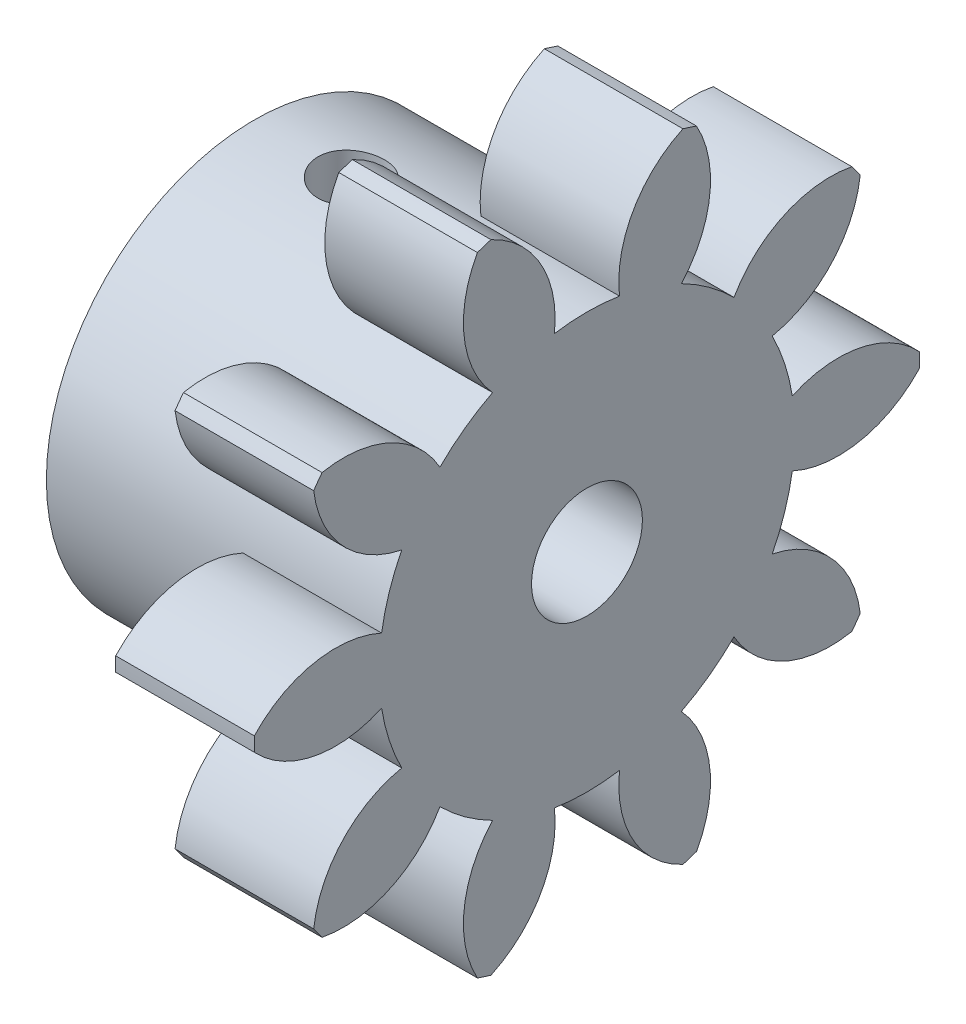
SolidWorks part; units mm, degrees
ref_plane "Plane1" through (0, 0, 0) normal (0, 0, 1) x (1, 0, 0)
ref_plane "Plane2" through (0, 0, 0) normal (0, 1, 0) x (1, 0, 0)
ref_plane "Plane3" through (0, 0, 0) normal (1, 0, 0) x (0, 0, -1)
sketch "HoldingSke" plane through (0, 0, 0) normal (0, 1, 0) x (1, 0, 0)
  line L0 (0, 0) -> (0.4924, -0.0868)
  line L1 (-15, 0) -> (100, 0) construction
  line L2 (0, 0) -> (-2.1039, 2.3779)
  line L3 (0, 0) -> (-11.863, 4.5341)
  line L4 (0, 0) -> (8.5048, 1.4996)
  line L5 (0, 0) -> (-18.7391, -6.9891)
  line L6 (0, 0) -> (-8.2896, -5.593)
  line L7 (-2.1039, 2.3779) -> (2.2011, 21.9091)
  line L8 (-76.2, 54.61) -> (-75.5, 54.61)
  line L9 (-71.009, 38.7566) -> (-53.1078, 45.2721)
  line L10 (-76.2, 71.12) -> (104.1128, 71.12)
  line L11 (0, 0) -> (-10, 0)
  line L12 (-76.2, 101.6) -> (-76.133, 101.6)
  line L13 (24.9733, 27.94) -> (52.9518, 28.4284)
  line L14 (24.9733, 27.94) -> (24.9743, 27.94)
  line L15 (24.9733, 27.94) -> (100.4006, 29.5858)
  line L16 (-63.627, -2) -> (-12.827, -2)
  circle A0 centre (0, 0) radius 2
  circle A1 centre (0, 0) radius 7.499
  circle A2 centre (0, 0) radius 25
  circle A3 centre (0, 0) radius 2
  dimension "MHD" = 14.998
  dimension "Hub_dia" = 50
  dimension "Bore" = 4
  dimension "MBD" = 4
  dimension "Num_teeth" = 10
  dimension "Pitch_radius" = 180.3128
  dimension "Pitch" = 0.5
  dimension "Width" = 10
  dimension "Overall_len" = 20
  dimension "Show_teeth" = 10
  dimension "Thickness" = 10
  dimension "OAL" = 20.0001
  dimension "T_dim" = 0.7
  dimension "Ap" = 20
  dimension "H" = 19.05
  dimension "Backlash" = 0.067
  dimension "Addendum_fac" = 1
  dimension "Dedendum_fac" = 1.25
  dimension "Clearance_fac" = 0.25
  dimension "Dedendum_add" = 0.001
  dimension "Module" = 2
sketch "BasProSke" plane through (0, 0, 0) normal (0, 1, 0) x (1, 0, 0)
  line L0 (-10, 0) -> (60, 0) construction
  line L1 (0, 0) -> (0, 12)
  line L2 (0, 0) -> (10, 0)
  line L3 (10, 0) -> (10, 12)
  line L4 (10, 12) -> (0, 12)
  dimension "Diameter" = 24
  dimension "Thickness" = 10
revolve "Base-Revolve" add sketch "BasProSke" angle 360 about L0
sketch "TooCutSke" plane through (0, 0, 0) normal (1, 0, 0) x (0, 0, -1)
  line L1 (0, 0) -> (0, 107) construction
  line L2 (0, 0) -> (-1.6814, 9.8576) construction
  line L3 (0, 0) -> (-6.1153, 18.8209) construction
  line L4 (-1.6814, 9.8576) -> (-3.0576, 9.4105) construction
  arc A0 (1.1737, 7.4066) -> (-1.1737, 7.4066) centre (0, 0) ccw
  arc A1 (3.4979, 11.5054) -> (-3.4979, 11.5054) centre (0, 0) ccw
  circle A2 centre (0, 0) radius 10 construction
  circle A3 centre (0, 0) radius 9.3969 construction
  arc A4 (-1.1737, 7.4066) -> (-3.4979, 11.5054) centre (-5.1477, 7.8615) ccw
  arc A5 (3.4979, 11.5054) -> (1.1737, 7.4066) centre (5.1477, 7.8615) ccw
  dimension "Root_dia" = 14.998
  dimension "Overcut_dia" = 24.0508
  dimension "Pitch_dia" = 20
  dimension "Base_dia" = 18.7939
  dimension "Flank_rad" = 4
  dimension "Half_ang" = 18
  dimension "Half_CT" = 1.4471
extrude "ToothCut" cut sketch "TooCutSke" along normal through all
fillet "Breaks" [suppressed] radius 0.04
fillet "RootFillets" [suppressed] radius 0.501
pattern_circular "TeethCuts" count 10 every 36 about axis through (-10, 0, 0) along (1, 0, 0) of "ToothCut", "RootFillets", "Breaks"
sketch "HubNeaOneSke" plane through (0, 0, 0) normal (-1, 0, 0) x (0, 0, 1)
  circle A0 centre (0, 0) radius 7.499
  dimension "Diameter" = 14.998
extrude "HubNearOne" add sketch "HubNeaOneSke" along normal blind 10.0001
sketch "HubNeaBotSke" plane through (0, 0, 0) normal (-1, 0, 0) x (0, 0, 1)
  circle A0 centre (0, 0) radius 7.499
  dimension "Diameter" = 14.998
extrude "HubNearBoth" [suppressed] add sketch "HubNeaBotSke" along normal blind 5
ref_plane "FarPln" through (10, 0, 0) normal (1, 0, 0) x (0, 0, -1)
sketch "HubFarSke" plane through (10, 0, 0) normal (1, 0, 0) x (0, 0, -1)
  circle A0 centre (0, 0) radius 7.499
  dimension "Diameter" = 14.998
extrude "HubFar" [suppressed] add sketch "HubFarSke" along normal blind 5
sketch "BorSke" plane through (0, 0, 0) normal (1, 0, 0) x (0, 0, -1)
  circle A0 centre (0, 0) radius 2
  dimension "Diameter" = 4
extrude "Bore" cut sketch "BorSke" along normal mid plane 40.0001
sketch "KeySke" plane through (0, 0, 0) normal (1, 0, 0) x (0, 0, -1)
  line L0 (-0.8, 0) -> (-0.8, 2.7)
  line L1 (-0.8, 2.7) -> (0.8, 2.7)
  line L2 (0.8, 2.7) -> (0.8, 0)
  line L3 (0, 0) -> (0, 34) construction
  line L4 (-0.8, 0) -> (0.8, 0)
  dimension "Offset" = 2.7
  dimension "Width" = 1.6
extrude "Keyway" [suppressed] cut sketch "KeySke" along normal mid plane 40.0001
pattern_circular "Keyway2" [suppressed] count 2 every 90 about axis through (-10, 0, 0) along (1, 0, 0)
sketch "Esquisse1" plane through (-10.0001, 0, 0) normal (-1, 0, 0) x (0, 0, 1)
  line L0 (0, 0) -> (0, 6.8885) construction
  line L1 (-2, 5.25) -> (2, 5.25)
  line L2 (-2, 5.25) -> (-2, 3.75)
  line L3 (-2, 3.75) -> (2, 3.75)
  line L4 (2, 5.25) -> (2, 3.75)
  line L5 (-2, 5.25) -> (2, 3.75) construction
  line L6 (-2, 3.75) -> (2, 5.25) construction
  point P0 (0, 4.5)
  dimension "D1" = 4
  dimension "D2" = 1.5
  dimension "D3" = 4.5
extrude "Enlèv. mat.-Extru.1" cut sketch "Esquisse1" against normal blind 10
sketch "Esquisse8" plane through (-10.0001, 0, 0) normal (-1, 0, 0) x (0, 0, 1)
  circle A0 centre (0, 0) radius 7.499
extrude "Enlèv. mat.-Extru.4" cut sketch "Esquisse8" against normal blind 3
hole_wizard "Dégagement M21" positions "Esquisse5" profile "Esquisse4" hole size "M2" standard "Ansi Métrique"
sketch "Esquisse5" plane through (0, 3.75, 0) normal (0, 1, 0) x (-1, 0, 0)
  line L1 (0.0001, -2) -> (7.0001, -2) construction
  line L2 (7.0001, 2) -> (7.0001, -2) construction
  point P0 (3.5001, 0)
  dimension "D1" = 3.5
  dimension "D2" = 2
sketch "Esquisse4" plane through (-3.5001, 3.75, 0) normal (1, 0, 0) x (0, 0, 1)
  line L0 (0, 0) -> (0, 3.721)
  line L1 (0, 3.721) -> (1.2, 3)
  line L2 (1.2, 3) -> (1.2, 0)
  line L5 (1.2, 0) -> (0, 0)
  line L10 (0, 3.721) -> (-1.2, 3) construction
  line L11 (0, -6.35) -> (0, 107.95) construction
  dimension "Diamètre du perçage" = 2.4
  dimension "Profondeur du perçage" = 3
  dimension "Angle de pointe" = 118
sketch "Esquisse6" plane through (0, 3.75, 0) normal (0, 1, 0) x (-1, 0, 0)
  line L0 (7.0001, 2) -> (7.0001, -2) construction
  circle A1 centre (3.5001, 0) radius 1.2
  dimension "D1" = 2.4
  dimension "D2" = 3.5
extrude "Enlèv. mat.-Extru.2" cut sketch "Esquisse6" along normal up to next
sketch "Esquisse7" plane through (10, 0, 0) normal (1, 0, 0) x (0, 0, -1)
  circle A0 centre (0, 0) radius 12
  dimension "D1" = 24
extrude "Enlèv. mat.-Extru.3" cut sketch "Esquisse7" against normal blind 5
equation "' \"Module@HoldingSke\" = 6.35"
equation "' \"Num_teeth@HoldingSke\" = 12"
equation "' \"Ap@HoldingSke\" =  20"
equation "' \"Width@HoldingSke\" = 0.5 * 25.4"
equation "' \"Hub_dia@HoldingSke\"= 1 * 25.4"
equation "' \"Overall_len@HoldingSke\" = 1.0 * 25.4"
equation "' \"Bore@HoldingSke\" = 0.75 * 25.4"
equation "' \"T_dim@HoldingSke\" = 0.1 * 25.4"
equation "' \"Width@KeySke\" = 0.25 * 25.4"
equation "' \"Show_teeth@HoldingSke\" = 13"
equation "' \"Backlash@HoldingSke\" = 0.009 * 25.4"
equation "' \"Addendum_fac@HoldingSke\" = 1.0"
equation "' \"Dedendum_fac@HoldingSke\" = 1.25"
equation "' \"Dedendum_add@HoldingSke\" = 0.00005 * 25.4"
equation "' \"Clearance_fac@HoldingSke\" = 0.25"
equation "\"Pitch@HoldingSke\" = 1 / \"Module@HoldingSke\""
equation "\"Overcut_dia@TooCutSke\" = (\"Num_teeth@HoldingSke\" + 2 * \"Addendum_fac@HoldingSke\") / \"Pitch@HoldingSke\" + 0.002 * 25.4"
equation "\"Pitch_dia@TooCutSke\" = \"Num_teeth@HoldingSke\" / \"Pitch@HoldingSke\""
equation "\"Base_dia@TooCutSke\" = \"Num_teeth@HoldingSke\" / \"Pitch@HoldingSke\" * cos((\"Ap@HoldingSke\"  * 3.14159265 / 180))"
equation "\"Root_dia@TooCutSke\" = (\"Num_teeth@HoldingSke\" + 2) / \"Pitch@HoldingSke\" - 2 * (\"Addendum_fac@HoldingSke\" + \"Dedendum_fac@HoldingSke\") / \"Pitch@HoldingSke\" - \"Dedendum_add@HoldingSke\" * 2"
equation "\"Half_ang@TooCutSke\" = 180 / \"Num_teeth@HoldingSke\""
equation "\"Half_CT@TooCutSke\" = \"Num_teeth@HoldingSke\" / \"Pitch@HoldingSke\" * sin((3.14159265 / 2 / \"Num_teeth@HoldingSke\")) / 2 - 7 * \"Backlash@HoldingSke\" / 4"
equation "\"Flank_rad@TooCutSke\" = \"Num_teeth@HoldingSke\" / \"Pitch@HoldingSke\" / 5"
equation "\"Radius@RootFillets\" = \"Clearance_fac@HoldingSke\" / \"Pitch@HoldingSke\" + \"Dedendum_add@HoldingSke\""
equation "\"Break_rad@Breaks\" = 0.02 / \"Pitch@HoldingSke\""
equation "\"Thickness@HoldingSke\" = \"Width@HoldingSke\""
equation "\"OAL@HoldingSke\" = \"Thickness@HoldingSke\""
equation "\"MHD@HoldingSke\" = (\"Num_teeth@HoldingSke\" + 2) / \"Pitch@HoldingSke\" - 2 * (\"Addendum_fac@HoldingSke\" + \"Dedendum_fac@HoldingSke\")  / \"Pitch@HoldingSke\" - \"Dedendum_add@HoldingSke\" * 2"
equation "\"MBD@HoldingSke\" = (\"Num_teeth@HoldingSke\" + 2) / \"Pitch@HoldingSke\" - 2 * (\"Addendum_fac@HoldingSke\" + \"Dedendum_fac@HoldingSke\")  / \"Pitch@HoldingSke\" - \"Dedendum_add@HoldingSke\" * 2 - 0.002 * 25.4"
equation "\"MHD@HoldingSke\" = ((sgn( \"MHD@HoldingSke\" - \"Hub_dia@HoldingSke\" )-1)*( \"MHD@HoldingSke\" - \"Hub_dia@HoldingSke\" ))/-2+ \"Hub_dia@HoldingSke\""
equation "\"MBD@HoldingSke\" = ((sgn( \"MBD@HoldingSke\" - \"Bore@HoldingSke\" )-1)*( \"MBD@HoldingSke\" - \"Bore@HoldingSke\" ))/-2+ \"Bore@HoldingSke\""
equation "\"OAL@HoldingSke\" = ((sgn( \"OAL@HoldingSke\" - \"Overall_len@HoldingSke\" )+1)*( \"OAL@HoldingSke\" - \"Overall_len@HoldingSke\" ))/2 + \"Overall_len@HoldingSke\" + 0.000002 * 25.4"
equation "\"Num_teeth@TeethCuts\" = int( \"Show_teeth@HoldingSke\" ) + 1"
equation "\"Num_teeth@TeethCuts\" = ((sgn( \"Num_teeth@TeethCuts\" - \"Num_teeth@HoldingSke\" )-1)*( \"Num_teeth@TeethCuts\" - \"Num_teeth@HoldingSke\" ))/-2+ \"Num_teeth@HoldingSke\""
equation "\"Num_teeth@TeethCuts\" = ((sgn( \"Num_teeth@TeethCuts\" - 2.0)+1)*( \"Num_teeth@TeethCuts\" - 2.0))/2 +2.0"
equation "\"Angle@TeethCuts\" = 360.0 / \"Num_teeth@HoldingSke\""
equation "\"Diameter@BasProSke\" = (\"Num_teeth@HoldingSke\" + 2 * \"Addendum_fac@HoldingSke\") / \"Pitch@HoldingSke\""
equation "\"Thickness@BasProSke\"  = \"Thickness@HoldingSke\""
equation "' \"Fillet_rad@BasProSke\" =  \"Thickness@HoldingSke\" * 0.05"
equation "\"MHD@HoldingSke\" = ((sgn( \"MHD@HoldingSke\" - \"Root_dia@TooCutSke\" )-1)*( \"MHD@HoldingSke\" - \"Root_dia@TooCutSke\" ))/-2+ \"Root_dia@TooCutSke\""
equation "\"Diameter@HubNeaOneSke\" = \"MHD@HoldingSke\""
equation "\"Length@HubNearOne\" = \"OAL@HoldingSke\" - \"Thickness@BasProSke\""
equation "\"Diameter@HubNeaBotSke\" = \"MHD@HoldingSke\""
equation "\"Length@HubNearBoth\" = ( \"OAL@HoldingSke\" - \"Thickness@BasProSke\" ) / 2.0"
equation "\"Thickness@FarPln\" = \"Thickness@BasProSke\""
equation "\"Diameter@HubFarSke\" = \"MHD@HoldingSke\""
equation "\"Length@HubFar\" = ( \"OAL@HoldingSke\" - \"Thickness@BasProSke\" ) / 2.0"
equation "\"Diameter@BorSke\" = \"MBD@HoldingSke\""
equation "\"D1@Bore\" = \"OAL@HoldingSke\" * 2.0"
equation "\"D1@Keyway\" = \"OAL@HoldingSke\" * 2.0"
equation "\"Offset@KeySke\" = \"T_dim@HoldingSke\" + \"MBD@HoldingSke\" / 2.0"
